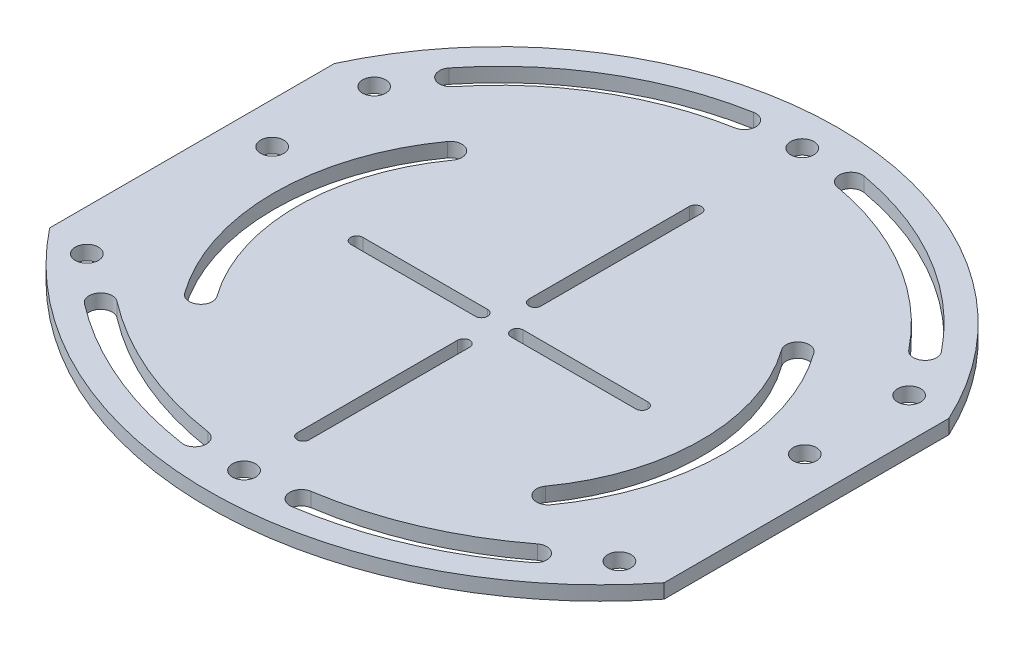
SolidWorks part; units mm, degrees
material "Acrylic (Medium-high impact)"
ref_plane "Front Plane" through (0, 0, 0) normal (0, 0, 1) x (1, 0, 0)
ref_plane "Top Plane" through (0, 0, 0) normal (0, 1, 0) x (1, 0, 0)
ref_plane "Right Plane" through (0, 0, 0) normal (1, 0, 0) x (0, 0, -1)
sketch "Sketch1" plane through (0, 0, 0) normal (0, 1, 0) x (1, 0, 0)
  line L0 (86.2, 39.9319) -> (86.2, -39.9319)
  line L5 (0, -1000) -> (0, 49000) construction
  line L6 (-86.2, 39.9319) -> (-86.2, -39.9319)
  arc A4 (-86.2, -39.9319) -> (86.2, -39.9319) centre (0, 0) ccw construction
  arc A5 (86.2, 39.9319) -> (-86.2, 39.9319) centre (0, 0) ccw
  arc A7 (-86.2, -39.9319) -> (86.2, -39.9319) centre (0, 28.4022) ccw
  dimension "D1" = 172.4
  dimension "D2" = 95
  dimension "D3" = 110
extrude "Boss-Extrude1" add sketch "Sketch1" along normal mid plane 4
sketch "Sketch2" plane through (0, 0, 0) normal (0, 1, 0) x (1, 0, 0)
  line L0 (0, -1000) -> (0, 49000) construction
  line L1 (-86.2, 39.9319) -> (-86.2, -39.9319) construction
  line L2 (-74.7, 11) -> (-74.7, -41) construction
  circle A0 centre (-74.7, 11) radius 3.25
  circle A1 centre (-74.7, -41) radius 3.25
  circle A2 centre (74.7, -41) radius 3.25
  circle A3 centre (74.7, 11) radius 3.25
  circle A4 centre (0, 0) radius 95 construction
  arc A5 (86.2, 39.9319) -> (-86.2, 39.9319) centre (0, 0) ccw construction
  circle A6 centre (0, -71.5978) radius 3.25
  arc A7 (-75.8168, -31.7008) -> (75.8168, -31.7008) centre (0, 28.4022) ccw construction
  circle A8 centre (0, 85) radius 3.25
  arc A9 (-80.9105, -35.7387) -> (-73.5655, -44.0456) centre (0, 28.4022) ccw construction
  arc A10 (14.4716, -67.2593) -> (15.4439, -73.6862) centre (14.9578, -70.4728) ccw
  arc A11 (-78.3636, -33.7197) -> (78.3636, -33.7197) centre (0, 28.4022) ccw
  arc A12 (-78.3636, -33.7197) -> (78.3636, -33.7197) centre (0, 28.4022) ccw construction
  arc A13 (62.9367, -53.4484) -> (58.9746, -48.2956) centre (60.9557, -50.872) ccw
  arc A14 (-75.0363, 39.9319) -> (75.0363, 39.9319) centre (0, 0) cw construction
  arc A15 (-75.8168, -31.7008) -> (-74.7, -33.0833) centre (0, 28.4022) ccw construction
  arc A16 (-80.9105, -35.7387) -> (80.9105, -35.7387) centre (0, 28.4022) ccw construction
  arc A17 (14.4716, -67.2593) -> (58.9746, -48.2956) centre (0, 28.4022) ccw
  arc A18 (15.4439, -73.6862) -> (62.9367, -53.4484) centre (0, 28.4022) ccw
  arc A19 (-62.9367, -53.4484) -> (-58.9746, -48.2956) centre (-60.9557, -50.872) cw
  arc A20 (-15.4439, -73.6862) -> (-62.9367, -53.4484) centre (0, 28.4022) cw
  arc A21 (-14.4716, -67.2593) -> (-15.4439, -73.6862) centre (-14.9578, -70.4728) cw
  arc A22 (-14.4716, -67.2593) -> (-58.9746, -48.2956) centre (0, 28.4022) cw
  arc A23 (-63.9416, 50.9365) -> (-69.0257, 54.9865) centre (-66.4836, 52.9615) cw
  arc A24 (-15.5128, 86.8759) -> (-69.0257, 54.9865) centre (0, 0) ccw
  arc A25 (15.5128, 86.8759) -> (14.3702, 80.4771) centre (14.9415, 83.6765) ccw
  arc A26 (63.9416, 50.9365) -> (69.0257, 54.9865) centre (66.4836, 52.9615) ccw
  arc A27 (14.3702, 80.4771) -> (63.9416, 50.9365) centre (0, 0) cw
  arc A28 (-15.5128, 86.8759) -> (-14.3702, 80.4771) centre (-14.9415, 83.6765) cw
  arc A29 (15.5128, 86.8759) -> (69.0257, 54.9865) centre (0, 0) cw
  arc A30 (-14.3702, 80.4771) -> (-63.9416, 50.9365) centre (0, 0) ccw
  circle A31 centre (-75.0363, 39.9319) radius 3.25
  circle A32 centre (75.0363, 39.9319) radius 3.25
  point P9 (-74.7, -15)
  dimension "D1" = 6.5
  dimension "D5" = 6.5
  dimension "D6" = 10
  dimension "D7" = 50
  dimension "D11" = 10
  dimension "D12" = 6.5
  dimension "D2" = 52
  dimension "D3" = 11.5
  dimension "D4" = 15
  dimension "D8" = 15
  dimension "D14" = 60
  dimension "D15" = 15
  dimension "D9" = 3.25
  dimension "D10" = 3.25
extrude "Cut-Holes" cut sketch "Sketch2" against normal through all both and the other way through all
sketch "Sketch3" plane through (0, 0, 0) normal (0, 1, 0) x (1, 0, 0)
  line L0 (-1000, 0) -> (49000, 0) construction
  line L1 (0, -1000) -> (0, 49000) construction
  line L2 (5, 1.7) -> (40, 1.7)
  line L3 (5, -1.7) -> (40, -1.7)
  line L4 (-5, -1.7) -> (-40, -1.7)
  line L5 (-5, 1.7) -> (-40, 1.7)
  line L6 (-1.7, 55) -> (-1.7, 10)
  line L7 (1.7, 10) -> (1.7, 55)
  line L8 (-1.7, -55) -> (-1.7, -10)
  line L9 (1.7, -10) -> (1.7, -55)
  circle A0 centre (0, 0) radius 60 construction
  arc A1 (-46.0942, 33.1042) -> (-51.3737, 36.8958) centre (-48.734, 35) ccw
  arc A2 (-51.3737, -36.8958) -> (-46.0942, -33.1042) centre (-48.734, -35) ccw
  arc A3 (-51.3737, 36.8958) -> (-51.3737, -36.8958) centre (0, 0) ccw
  arc A4 (-46.0942, 33.1042) -> (-46.0942, -33.1042) centre (0, 0) ccw
  arc A5 (51.3737, -36.8958) -> (46.0942, -33.1042) centre (48.734, -35) cw
  arc A6 (46.0942, 33.1042) -> (46.0942, -33.1042) centre (0, 0) cw
  arc A7 (51.3737, 36.8958) -> (51.3737, -36.8958) centre (0, 0) cw
  arc A8 (46.0942, 33.1042) -> (51.3737, 36.8958) centre (48.734, 35) cw
  arc A9 (5, 1.7) -> (5, -1.7) centre (5, 0) ccw
  arc A10 (-5, 1.7) -> (-5, -1.7) centre (-5, 0) cw
  arc A11 (40, -1.7) -> (40, 1.7) centre (40, 0) ccw
  arc A12 (-40, -1.7) -> (-40, 1.7) centre (-40, 0) cw
  arc A13 (-1.7, 10) -> (1.7, 10) centre (0, 10) ccw
  arc A14 (1.7, 55) -> (-1.7, 55) centre (0, 55) ccw
  arc A15 (1.7, -55) -> (-1.7, -55) centre (0, -55) cw
  arc A16 (-1.7, -10) -> (1.7, -10) centre (0, -10) cw
  dimension "D1" = 120
  dimension "D2" = 6.5
  dimension "D3" = 70
  dimension "D4" = 3.4
  dimension "D5" = 10
  dimension "D6" = 35
  dimension "D7" = 45
  dimension "D8" = 20
extrude "Cut-Extrude1" cut sketch "Sketch3" against normal through all both and the other way through all
